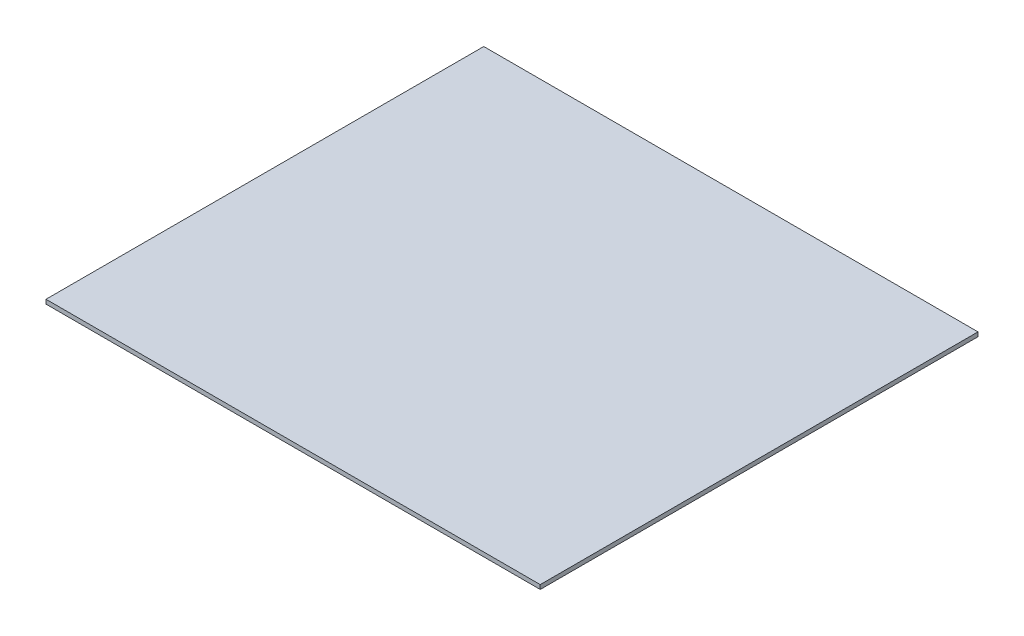
SolidWorks part; units mm, degrees
ref_plane "Front Plane" through (0, 0, 0) normal (0, 0, 1) x (1, 0, 0)
ref_plane "Top Plane" through (0, 0, 0) normal (0, 1, 0) x (1, 0, 0)
ref_plane "Right Plane" through (0, 0, 0) normal (1, 0, 0) x (0, 0, -1)
sketch "Sketch1" plane through (0, 0, 0) normal (0, 1, 0) x (1, 0, 0)
  line L1 (-175, -155) -> (175, -155)
  line L2 (-175, -155) -> (-175, 155)
  line L3 (-175, 155) -> (175, 155)
  line L4 (175, -155) -> (175, 155)
  line L5 (-175, -155) -> (175, 155) construction
  line L6 (-175, 155) -> (175, -155) construction
  point P0 (0, 0)
  dimension "D1" = 310
  dimension "D2" = 350
extrude "Boss-Extrude1" add sketch "Sketch1" along normal blind 3
